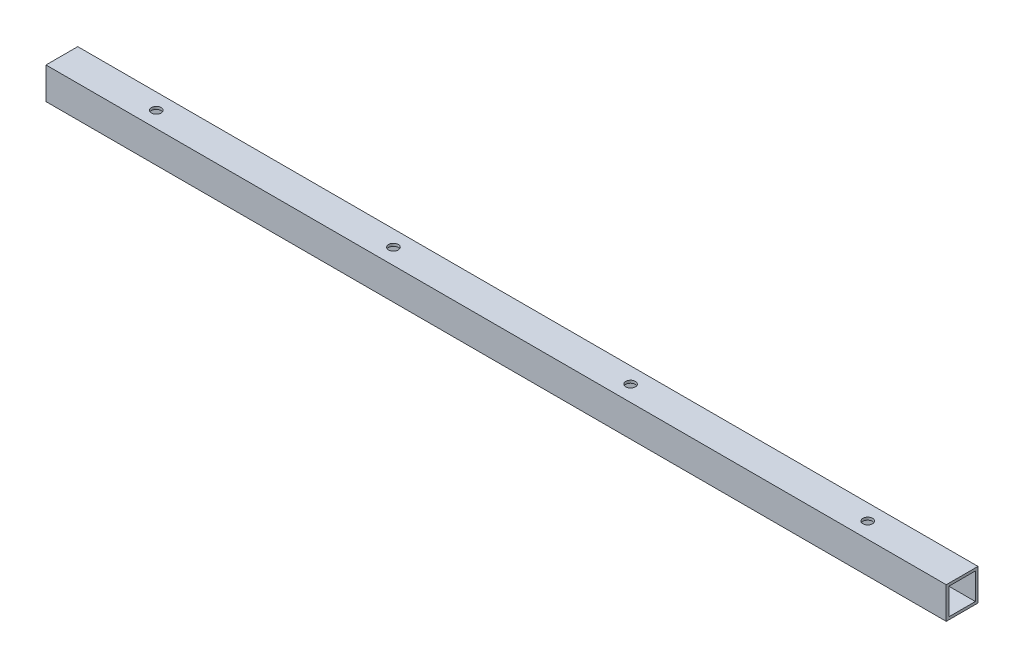
SolidWorks part; units mm, degrees
material "1060 Alloy"
ref_plane "Front Plane" through (0, 0, 0) normal (0, 0, 1) x (1, 0, 0)
ref_plane "Top Plane" through (0, 0, 0) normal (0, 1, 0) x (1, 0, 0)
ref_plane "Right Plane" through (0, 0, 0) normal (1, 0, 0) x (0, 0, -1)
sketch "Sketch1" plane through (0, 0, 0) normal (1, 0, 0) x (0, -1, 0)
  line L1 (-9.525, 9.525) -> (9.525, 9.525)
  line L2 (-9.525, 9.525) -> (-9.525, -9.525)
  line L3 (-9.525, -9.525) -> (9.525, -9.525)
  line L4 (9.525, 9.525) -> (9.525, -9.525)
  line L5 (-9.525, 9.525) -> (9.525, -9.525) construction
  line L6 (-9.525, -9.525) -> (9.525, 9.525) construction
  line L7 (-7.9375, 7.9375) -> (7.9375, 7.9375)
  line L8 (-7.9375, 7.9375) -> (-7.9375, -7.9375)
  line L9 (-7.9375, -7.9375) -> (7.9375, -7.9375)
  line L10 (7.9375, 7.9375) -> (7.9375, -7.9375)
  line L11 (-7.9375, 7.9375) -> (7.9375, -7.9375) construction
  line L12 (-7.9375, -7.9375) -> (7.9375, 7.9375) construction
  point P0 (0, 0)
  point P5 (0, 0)
  dimension "D2" = 19.05
  dimension "D1" = 15.875
extrude "Tube" add sketch "Sketch1" along normal blind 539.9532
sketch "Sketch3" plane through (0, 9.525, 0) normal (0, 1, 0) x (1, 0, 0)
  line L0 (0, 0) -> (-19.05, 0) construction
  line L1 (-19.05, 0) -> (-22.1234, 0) construction
  line L2 (0, 0) -> (56.6166, 0) construction
  circle A0 centre (56.6166, 0) radius 2.8956
  dimension "D1" = 5.7912
  dimension "D2" = 3.0734
  dimension "D3" = 19.05
  dimension "D4" = 78.74
extrude "RearTopHoleMaster" cut sketch "Sketch3" against normal through all
pattern_linear "LPattern2" count 4 spacing 142.24 along (1, 0, 0) of "RearTopHoleMaster"
equation "\"Height\"= 32in"
equation "\"Width\"= 23in"
equation "\"Depth\"= 20in"
equation "\"Plexi\"= .121in"
equation "\"Cutwidth\"= .016in"
equation "\"Earsize\"= 1in + \"Cutwidth\" /2"
equation "\"Slotsize\" = 1in - \"CutWidth\" / 2"
equation "\"InnerHeight\" = \"Height\" -2 * \"Plexi\""
equation "\"InnerWidth\" = \"Width\" - 2* \"Plexi\""
equation "\"RearHoleSpacing\" = (\"Width\" - 2*\"RearHolesBorder\") / (\"RearNumHoles\"-1)"
equation "\"Boxsize\" = .75in"
equation "\"Boxinner\" = .625in"
equation "\"InnerDepth\" = \"Depth\" - 2*\"Plexi\""
equation "\"RearNumHoles\" = 4"
equation "\"RearHolesBorder\" = 2.25"
equation "\"SideVertNumHoles\" = 4"
equation "\"SideVertHolesBorder\" = \"CornerCube\"+\"FingerLength\"+1.50"
equation "\"RivetDia\" = .228in"
equation "\"SlotDepth\" = \"Plexi\" + 0.75in + .005in"
equation "\"SideSlotWidth\"   = \"Plexi\"+.005in"
equation "\"SidePanelVertSpacing\" = (\"Height\"-2*(1.75-\"Plexi\")) / 5"
equation "\"BottomPanelSideHoleSpacing\" = (\"InnerDepth\"-2*(1.75-\"Plexi\")) / 4"
equation "\"D2@Sketch1\"=\"Boxsize\""
equation "\"D1@Sketch1\"=\"Boxinner\""
equation "\"CornerCube\" = 0.75in"
equation "\"RearBarLength\" = (\"InnerWidth\"-2*\"CornerCube\")"
equation "\"D1@Tube\"=\"RearBarLength\""
equation "\"D1@Sketch3\"=\"RivetDia\""
equation "\"D2@Sketch3\"=\"Plexi\""
equation "\"D3@Sketch3\"=\"CornerCube\""
equation "\"RearTopNumHoles\" = 4"
equation "\"RearTopHolesBorder\" = 3.1"
equation "\"RearTopHolesSpacing\" = (\"Width\" - 2*\"RearTopHolesBorder\") / (\"RearTopNumHoles\"-1)"
equation "\"SideVertHoleSpacing\" = (\"InnerHeight\" - 2*\"SideVertHolesBorder\") / (\"SideVertNumHoles\"-1)"
equation "\"D4@Sketch3\"=\"RearTopHolesBorder\""
equation "\"D3@LPattern2\"=\"RearTopHolesSpacing\""
equation "\"D1@LPattern2\"=\"RearTopNumHoles\""
